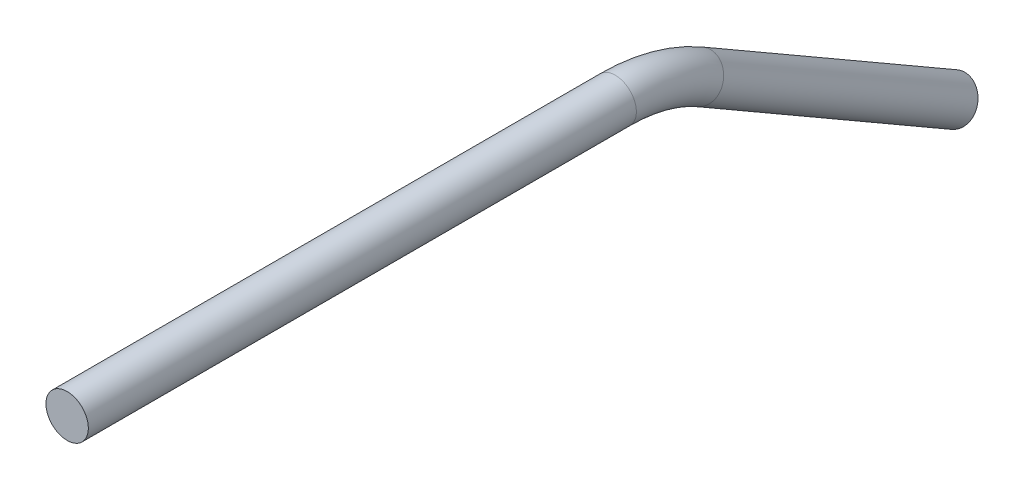
SolidWorks part; units mm, degrees
ref_plane "Front Plane" through (0, 0, 0) normal (0, 0, 1) x (1, 0, 0)
ref_plane "Top Plane" through (0, 0, 0) normal (0, 1, 0) x (1, 0, 0)
ref_plane "Right Plane" through (0, 0, 0) normal (1, 0, 0) x (0, 0, -1)
sketch "Sketch2" plane through (0, 0, 0) normal (0, 0, 1) x (1, 0, 0)
  circle A0 centre (0, 0) radius 3.175
  dimension "D1" = 6.35
sketch "Sketch4" plane through (0, 0, 0) normal (1, 0, 0) x (0, 0, -1)
  line L0 (0, 0) -> (82.0941, 0)
  line L1 (94.7941, -3.403) -> (132.8941, -25.4)
  arc A0 (94.7941, -3.403) -> (82.0941, 0) centre (82.0941, -25.4) ccw
  point P6 (88.9, 0)
  dimension "D4" = 25.4
  dimension "D1" = 88.9
  dimension "D2" = 50.8
  dimension "D3" = 30
sweep "Sweep1" add profiles "Sketch2" path "Sketch4"
